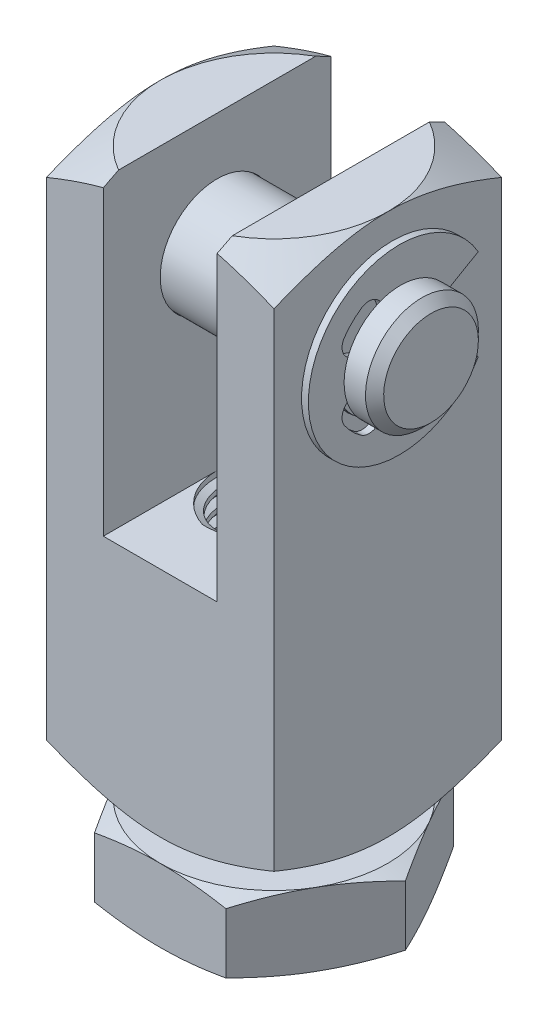
SolidWorks part; units mm, degrees
ref_plane "Front" through (0, 0, 0) normal (0, 0, 1) x (1, 0, 0)
ref_plane "Top" through (0, 0, 0) normal (0, 1, 0) x (1, 0, 0)
ref_plane "Right" through (0, 0, 0) normal (1, 0, 0) x (0, 0, -1)
sketch "Sketch1" plane through (0, 0, 0) normal (0, 0, 1) x (1, 0, 0)
  line L1 (-6.35, 0) -> (6.35, 0)
  line L2 (-6.35, 0) -> (-6.35, 30.226)
  line L3 (-6.35, 30.226) -> (6.35, 30.226)
  line L4 (6.35, 0) -> (6.35, 30.226)
  dimension "Height" = 30.226
  dimension "Width" = 12.7
extrude "Extrude1" add sketch "Sketch1" along normal mid plane 12.7
sketch "Sketch2" plane through (0, 0, 0) normal (0, 0, 1) x (1, 0, 0)
  line L0 (-6.35, 30.226) -> (6.35, 30.226) construction
  line L1 (-3.175, 30.226) -> (3.175, 30.226)
  line L2 (-3.175, 30.226) -> (-3.175, 12.954)
  line L3 (-3.175, 12.954) -> (3.175, 12.954)
  line L4 (3.175, 30.226) -> (3.175, 12.954)
  line L5 (0, 0) -> (0, 12.954) construction
  dimension "Slot Width" = 6.35
  dimension "Slot Height" = 17.272
extrude "Cut-Extrude1" cut sketch "Sketch2" against normal through all and the other way through all
sketch "Sketch9" plane through (0, 0, 0) normal (0, 0, 1) x (1, 0, 0)
  line L0 (6.35, 0) -> (6.35, 30.226) construction
  line L1 (-6.35, 27.051) -> (6.35, 27.051)
  line L2 (-6.35, 27.051) -> (-6.35, 23.876)
  line L3 (-6.35, 23.876) -> (6.35, 23.876)
  line L4 (6.35, 27.051) -> (6.35, 23.876)
  line L5 (-6.35, 0) -> (-6.35, 30.226) construction
  line L6 (-6.35, 30.226) -> (6.35, 30.226) construction
  line L7 (-6.35, 23.876) -> (-9.525, 23.876) construction
  dimension "Pin Dist" = 6.35
  dimension "Pin Dia" = 6.35
revolve "Cut-Revolve3" cut sketch "Sketch9" angle 360 about L7
sketch "Sketch4" plane through (0, 30.226, 0) normal (0, 1, 0) x (-1, 0, 0)
  circle A0 centre (0, 0) radius 6.35
extrude "Cut-Extrude3" cut sketch "Sketch4" against normal through all draft 60 flip side to cut
sketch "Sketch5" plane through (0, 0, 0) normal (0, 1, 0) x (1, 0, 0)
  circle A0 centre (0, 0) radius 6.35 construction
  circle A1 centre (0, 0) radius 6.35
extrude "Cut-Extrude4" cut sketch "Sketch5" along normal through all draft 60 flip side to cut
sketch "Sketch6" plane through (0, 0, 0) normal (0, 0, 1) x (1, 0, 0)
  line L0 (0, 0) -> (0, 12.954) construction
  line L1 (0, 0) -> (3.175, 0)
  line L2 (0, 0) -> (0, 12.954)
  line L3 (0, 12.954) -> (3.175, 12.954)
  line L4 (3.175, 0) -> (3.175, 12.954)
  line L5 (-3.175, 12.954) -> (3.175, 12.954) construction
  line L6 (0, 0) -> (0, -3.175) construction
  line L7 (-3.175, 0) -> (-3.175, 12.954) construction
  dimension "Thread Dia" = 6.35
revolve "Revolve1" add sketch "Sketch6" angle 360 about L6
sketch "Sketch7" plane through (0, 0, 0) normal (0, 0, 1) x (1, 0, 0)
  line L0 (-3.175, 0) -> (3.175, 0) construction
  line L1 (3.175, 0) -> (3.175, 0.9071) construction
  line L2 (3.175, 0.9071) -> (-3.175, 0) construction
  line L3 (-3.175, 0) -> (-3.191, 0.1123) construction
  line L4 (-3.191, 0.1123) -> (-3.3033, 0.898)
  line L5 (-3.3033, 0.898) -> (-2.7771, 0.6868)
  line L6 (-2.7771, 0.6868) -> (-2.7451, 0.4623)
  line L7 (-2.7451, 0.4623) -> (-3.191, 0.1123)
  line L8 (-2.7611, 0.5746) -> (-3.2472, 0.5051) construction
  line L9 (-3.175, 0) -> (-3.175, 0.5154) construction
  line L10 (-3.175, 0.5154) -> (3.175, 1.4226) construction
  line L11 (3.175, 1.4226) -> (3.175, 0.9071) construction
  line L12 (-3.175, 0) -> (-3.175, 12.954) construction
  line L13 (-3.175, 0) -> (3.175, 0) construction
  line L14 (3.175, 0) -> (3.175, 12.954) construction
  line L15 (0.1384, 0) -> (-0.1384, 1.938) construction
  point P19 (0, 0.969)
  dimension "D1" = 0.1134
  dimension "D2" = 0.2268
  dimension "D3" = 0.9071
  dimension "Thread Pitch" = 0.9071
  dimension "D4" = 60
revolve "Cut-Revolve1" cut sketch "Sketch7" angle 360 about L15
pattern_linear "LPattern1" count 2 spacing 0.9071 along (0, -1, 0) count 14 spacing 0.9071 along (0, 1, 0) of "Cut-Revolve1"
sketch "Sketch8" plane through (0, 0, 0) normal (0, 0, 1) x (1, 0, 0)
  line L0 (3.175, 0) -> (0, 1.8331)
  line L1 (0, 1.8331) -> (0, 0)
  line L2 (0, 0) -> (3.175, 0)
  dimension "D1" = 30
revolve "Cut-Revolve2" cut sketch "Sketch8" angle 360 about L1
combine bodies "Combine1" operation type subtract main body 117 bodies to subtract 116
ref_plane "Plane1" through (0, -1.27, 0) normal (0, 1, 0) x (-1, 0, 0)
sketch "Sketch10" plane through (0, -1.27, 0) normal (0, 1, 0) x (-1, 0, 0)
  line L1 (-7.3323, 0) -> (-3.6662, -6.35)
  line L2 (-3.6662, -6.35) -> (3.6662, -6.35)
  line L3 (3.6662, -6.35) -> (7.3323, 0)
  line L4 (7.3323, 0) -> (3.6662, 6.35)
  line L5 (3.6662, 6.35) -> (-3.6662, 6.35)
  line L6 (-3.6662, 6.35) -> (-7.3323, 0)
  circle A0 centre (0, 0) radius 6.35 construction
  dimension "D1" = 12.7
extrude "Extrude2" add sketch "Sketch10" against normal blind 4.064 separate body
sketch "Sketch11" plane through (0, 0, 0) normal (0, 0, 1) x (1, 0, 0)
  line L0 (6.35, -1.27) -> (7.3323, -1.27)
  line L1 (7.3323, -1.27) -> (7.3323, -1.6275)
  line L2 (7.3323, -1.6275) -> (6.35, -1.27)
  line L3 (6.35, -5.334) -> (7.3323, -5.334)
  line L4 (7.3323, -5.334) -> (7.3323, -4.9765)
  line L5 (7.3323, -4.9765) -> (6.35, -5.334)
  line L6 (6.35, -1.27) -> (6.35, -5.334) construction
  line L7 (7.3323, -5.334) -> (7.3323, -1.27) construction
  line L8 (3.6662, -5.334) -> (7.3323, -5.334) construction
  line L11 (6.35, -1.27) -> (0, -1.27) construction
  line L12 (6.35, -1.27) -> (-6.35, -1.27) construction
  line L13 (0, -1.27) -> (0, -5.334) construction
  line L14 (0, -5.334) -> (6.35, -5.334) construction
  dimension "D1" = 20
revolve "Cut-Revolve4" cut sketch "Sketch11" angle 360 about L13
sketch "Sketch12" plane through (0, 0, 0) normal (0, 0, 1) x (1, 0, 0)
  line L0 (3.175, 0) -> (3.175, 12.954) construction
  line L1 (0, -1.27) -> (3.175, -1.27)
  line L2 (0, -1.27) -> (0, -5.334)
  line L3 (0, -5.334) -> (3.175, -5.334)
  line L4 (3.175, -1.27) -> (3.175, -5.334)
  line L5 (0, 0) -> (0, 12.954) construction
  line L6 (6.35, -1.27) -> (0, -1.27) construction
  line L7 (0, -5.334) -> (6.35, -5.334) construction
  line L8 (0, -5.334) -> (0, 0) construction
  line L9 (-3.175, -1.27) -> (-3.175, -5.334) construction
revolve "Revolve2" add sketch "Sketch12" angle 360 about L2
sketch "Sketch13" plane through (0, 0, 0) normal (0, 0, 1) x (1, 0, 0)
  line L0 (-3.175, -5.334) -> (3.175, -5.334) construction
  line L1 (3.175, -5.334) -> (3.175, -4.4269) construction
  line L2 (3.175, -4.4269) -> (-3.175, -5.334) construction
  line L3 (-3.175, -5.334) -> (-3.191, -5.2217) construction
  line L4 (-3.191, -5.2217) -> (-3.3033, -4.436)
  line L5 (-3.3033, -4.436) -> (-2.7771, -4.6472)
  line L6 (-2.7771, -4.6472) -> (-2.7451, -4.8717)
  line L7 (-2.7451, -4.8717) -> (-3.191, -5.2217)
  line L8 (-2.7611, -4.7594) -> (-3.2472, -4.8289) construction
  line L9 (-3.175, -5.334) -> (-3.175, -4.8186) construction
  line L10 (-3.175, -4.8186) -> (3.175, -3.9114) construction
  line L11 (3.175, -3.9114) -> (3.175, -4.4269) construction
  line L15 (-3.175, -1.27) -> (-3.175, -5.334) construction
  line L16 (0, -5.334) -> (3.175, -5.334) construction
  line L17 (3.175, -1.27) -> (3.175, -5.334) construction
  line L18 (0.1384, -5.334) -> (-0.1384, -3.396) construction
  point P19 (0, -4.365)
  dimension "D1" = 0.1134
  dimension "D2" = 0.2268
  dimension "D3" = 0.9071
  dimension "D4" = 60
  dimension "D5" = 0.9071
revolve "Cut-Revolve5" cut sketch "Sketch13" angle 360 about L18
pattern_linear "LPattern3" count 2 spacing 0.9071 along (0, -1, 0) count 4 spacing 0.9071 along (0, 1, 0) of "Cut-Revolve5"
sketch "Sketch14" plane through (0, -1.27, 0) normal (0, 1, 0) x (-1, 0, 0)
  circle A0 centre (0, 0) radius 3.175
extrude "Cut-Extrude5" cut sketch "Sketch14" against normal through all draft 60
sketch "Sketch15" plane through (0, -5.334, 0) normal (0, -1, 0) x (1, 0, 0)
  circle A0 centre (0, 0) radius 3.175 construction
  circle A1 centre (0, 0) radius 3.175
extrude "Cut-Extrude6" cut sketch "Sketch15" against normal through all draft 60
combine bodies "Combine2" operation type subtract main body 126 bodies to subtract 124
sketch "Sketch16" plane through (0, 0, 0) normal (0, 0, 1) x (1, 0, 0)
  line L0 (0, 0) -> (0, 27.0256) construction
  line L1 (-8.255, 27.0256) -> (-7.0612, 27.0256)
  line L2 (8.763, 26.5176) -> (8.763, 23.876)
  line L3 (8.763, 23.876) -> (-8.763, 23.876)
  line L4 (-8.763, 23.876) -> (-8.763, 26.5176)
  line L5 (7.0612, 27.0256) -> (8.255, 27.0256)
  line L6 (8.763, 23.876) -> (11.3937, 23.876) construction
  line L7 (-6.35, 27.051) -> (6.35, 27.051) construction
  line L8 (-6.35, 23.876) -> (-9.525, 23.876) construction
  line L9 (-6.35, 28.7074) -> (-6.35, 1.5186) construction
  line L10 (-7.0612, 27.0256) -> (-7.0612, 26.2636)
  line L11 (-7.0612, 26.2636) -> (-6.5532, 26.2636)
  line L13 (-6.5532, 27.0256) -> (-6.5532, 26.2636)
  line L17 (6.5532, 27.0256) -> (6.5532, 26.2636)
  line L18 (6.5532, 26.2636) -> (7.0612, 26.2636)
  line L19 (7.0612, 27.0256) -> (7.0612, 26.2636)
  line L20 (-6.5532, 27.0256) -> (6.5532, 27.0256)
  line L22 (-8.763, 26.5176) -> (-8.255, 27.0256)
  line L23 (8.255, 27.0256) -> (8.763, 26.5176)
  point P0 (-8.763, 27.0256)
  point P3 (8.763, 27.0256)
  point P28 (-6.8072, 26.2636)
  dimension "D1" = 17.526
  dimension "D2" = 0.0254
  dimension "D3" = 0.2032
  dimension "D4" = 0.508
  dimension "D5" = 0.762
revolve "Revolve3" add sketch "Sketch16" angle 360 about L6
ref_plane "Plane2" through (-6.8072, 0, 0) normal (1, 0, 0) x (0, 0, -1)
sketch "Sketch17" plane through (-6.8072, 0, 0) normal (1, 0, 0) x (0, 0, -1)
  line L0 (2.0677, 25.0698) -> (4.3994, 26.416)
  line L1 (2.0677, 22.6822) -> (4.3994, 21.336)
  line L2 (0, 23.876) -> (-3.5921, 27.4681) construction
  line L3 (0, 23.876) -> (0, 26.5176) construction
  line L4 (-0.8166, 26.1196) -> (-0.9824, 26.5752)
  line L5 (-2.2436, 24.6926) -> (-2.6992, 24.8584)
  line L6 (0, 23.876) -> (3.175, 23.876) construction
  line L7 (-2.2436, 23.0594) -> (-2.6992, 22.8936)
  line L8 (-0.8166, 21.6324) -> (-0.9824, 21.1768)
  arc A0 (4.3994, 26.416) -> (4.3994, 21.336) centre (0, 23.876) ccw
  arc A1 (2.0677, 25.0698) -> (-0.8166, 26.1196) centre (0, 23.876) ccw
  arc A2 (-2.134, 26.9399) -> (-3.0639, 26.01) centre (0, 23.876) ccw
  arc A3 (-2.2436, 24.6926) -> (-2.2436, 23.0594) centre (0, 23.876) ccw
  arc A4 (-0.9824, 26.5752) -> (-2.134, 26.9399) centre (-1.6985, 26.3146) ccw
  arc A5 (-2.6992, 24.8584) -> (-3.0639, 26.01) centre (-2.4386, 25.5745) cw
  circle A6 centre (0, 23.876) radius 3.175 construction
  arc A7 (-2.6992, 22.8936) -> (-3.0639, 21.742) centre (-2.4386, 22.1775) ccw
  arc A8 (-0.9824, 21.1768) -> (-2.134, 20.8121) centre (-1.6985, 21.4374) cw
  arc A9 (-2.134, 20.8121) -> (-3.0639, 21.742) centre (0, 23.876) cw
  arc A10 (-0.8166, 21.6324) -> (2.0677, 22.6822) centre (0, 23.876) ccw
  point P1 (3.2336, 25.7429)
  dimension "D2" = 5.08
  dimension "D6" = 0.762
  dimension "D1" = 60
  dimension "D3" = 45
  dimension "D4" = 25
  dimension "D5" = 25
extrude "Extrude3" add sketch "Sketch17" along normal mid plane 0.381
mirror "Mirror1" about plane through (0, 0, 0) normal (1, 0, 0) of "Extrude3"
equation "\"D1@Extrude1\"=\"Width@Sketch1\""
equation "\"D1@Sketch7\"=\"Thread Pitch@Sketch7\"/8"
equation "\"D2@Sketch7\"=\"Thread Pitch@Sketch7\"/4"
equation "\"D3@Sketch7\"=\"Thread Pitch@Sketch7\""
equation "\"D3@LPattern1\"=\"Thread Pitch@Sketch7\""
equation "\"D4@LPattern1\"=\"Thread Pitch@Sketch7\""
equation "\"D2@LPattern1\"=(\"Height@Sketch1\"-\"Slot Height@Sketch2\")/\"Thread Pitch@Sketch7\""
equation "\"D1@Sketch10\"=\"Width@Sketch1\""
equation "\"D3@Sketch13\"=\"Thread Pitch@Sketch7\""
equation "\"D1@Sketch13\"=\"D1@Sketch7\""
equation "\"D2@Sketch13\"=\"D2@Sketch7\""
equation "\"D5@Sketch13\"=\"D3@Sketch7\""
equation "\"D4@LPattern3\"=\"Thread Pitch@Sketch7\""
equation "\"D3@LPattern3\"=\"Thread Pitch@Sketch7\""
equation " \"D2@LPattern3\"=\"Nut Height@Extrude2\"/\"Thread Pitch@Sketch7\""
